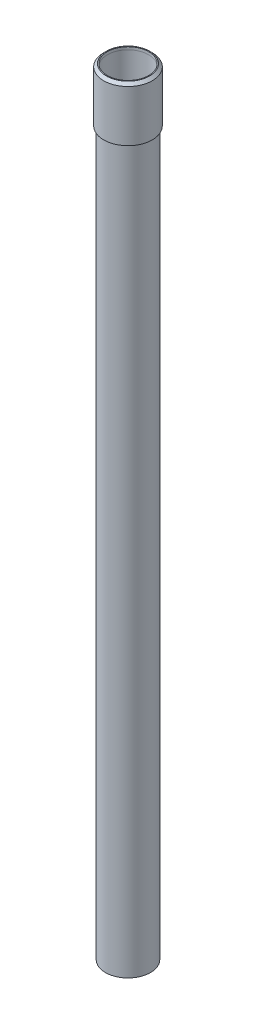
SolidWorks part; units mm, degrees
ref_plane "Front Plane" through (0, 0, 0) normal (0, 0, 1) x (1, 0, 0)
ref_plane "Top Plane" through (0, 0, 0) normal (0, 1, 0) x (1, 0, 0)
ref_plane "Right Plane" through (0, 0, 0) normal (1, 0, 0) x (0, 0, -1)
sketch "Sketch1" plane through (0, 0, 0) normal (0, 1, 0) x (1, 0, 0)
  circle A0 centre (0, 0) radius 12.5
  circle A1 centre (0, 0) radius 11.5
  dimension "D1" = 25
  dimension "D2" = 1
extrude "Extrude1" add sketch "Sketch1" along normal mid plane 430
sketch "Sketch2" plane through (0, 0, 0) normal (0, 0, 1) x (1, 0, 0)
  line L0 (0, 224.3248) -> (0, 181.7869) construction
  line L1 (13.5, 216.5) -> (13.5, 186.5)
  line L3 (11.5, -215) -> (11.5, 215) construction
  line L4 (12.5, 216.5) -> (-12.5, 216.5)
  line L5 (13.5, 216.5) -> (11.5, 216.5)
  line L6 (11.5, 215) -> (11.5, 216.5)
  line L9 (13.5, 186.5) -> (12.5, 186.5)
  line L10 (12.5, 215) -> (-12.5, 215) construction
  line L11 (12.5, -215) -> (12.5, 215) construction
  line L12 (12.5, 215) -> (11.5, 215)
  line L13 (12.5, 186.5) -> (12.5, 215)
  dimension "D1" = 27
  dimension "D3" = 30
  dimension "D2" = 1.5
revolve "Revolve1" add sketch "Sketch2" angle 360 about L0
chamfer "Chamfer1" distance 1.5 angle 45 1 edges at (0, 216.5, 13.5)
